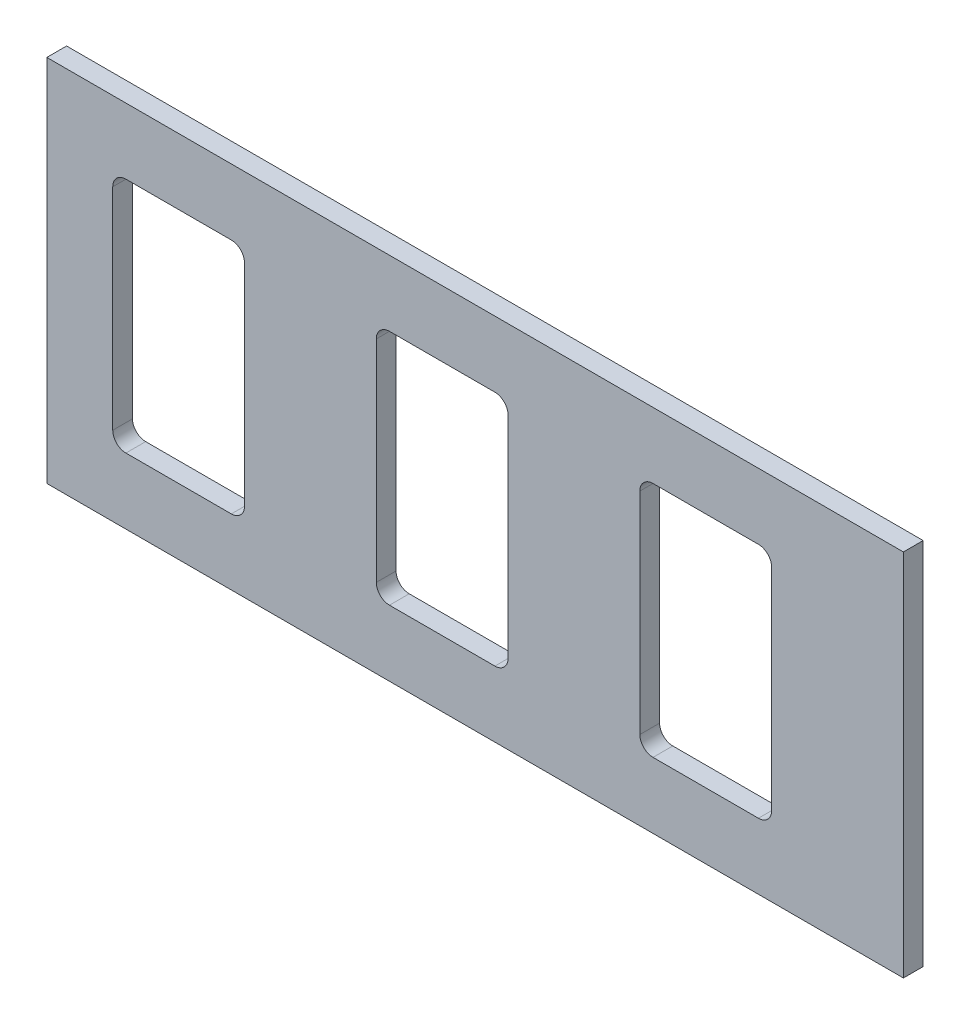
SolidWorks part; units mm, degrees
ref_plane "Front Plane" through (0, 0, 0) normal (0, 0, 1) x (1, 0, 0)
ref_plane "Top Plane" through (0, 0, 0) normal (0, 1, 0) x (1, 0, 0)
ref_plane "Right Plane" through (0, 0, 0) normal (1, 0, 0) x (0, 0, -1)
sketch "Sketch1" plane through (0, 0, 0) normal (0, 0, 1) x (1, 0, 0)
  line L1 (65, -28) -> (-65, -28)
  line L2 (65, -28) -> (65, 28)
  line L3 (65, 28) -> (-65, 28)
  line L4 (-65, -28) -> (-65, 28)
  line L5 (65, -28) -> (-65, 28) construction
  line L6 (65, 28) -> (-65, -28) construction
  point P0 (0, 0)
extrude "Boss-Extrude1" add sketch "Sketch1" along normal blind 3
sketch "Sketch2" plane through (0, 0, 3) normal (0, 0, 1) x (1, 0, 0)
  line L1 (25, -18) -> (25, 18)
  line L2 (45, -28) -> (45, 28)
  line L3 (45, -18) -> (45, 18)
  line L4 (5, -18) -> (5, 18)
  line L5 (-15, -18) -> (-15, 18)
  line L6 (-35, -18) -> (-35, 18)
  line L7 (-55, -18) -> (-55, 18)
  line L10 (65, 18) -> (-65, 18)
  line L11 (45, 18) -> (25, 18)
  line L12 (5, 18) -> (-15, 18)
  line L13 (-65, -18) -> (65, -18)
  line L14 (-55, -18) -> (-35, -18)
  line L15 (25, -18) -> (45, -18)
  line L16 (-35, 18) -> (-55, 18)
  line L17 (-15, -18) -> (5, -18)
  dimension "D1" = 20
  dimension "D2" = 10
  dimension "D3" = 10
extrude "Cut-Extrude1" cut sketch "Sketch2" against normal blind 5
fillet "Fillet1" radius 2 12 edges at (25, 18, 1.5) (-15, 18, 1.5) (-55, 18, 1.5) (-35, 18, 1.5) (5, 18, 1.5) (45, 18, 1.5) (-35, -18, 1.5) (5, -18, 1.5) (45, -18, 1.5) (25, -18, 1.5) (-15, -18, 1.5) (-55, -18, 1.5)
